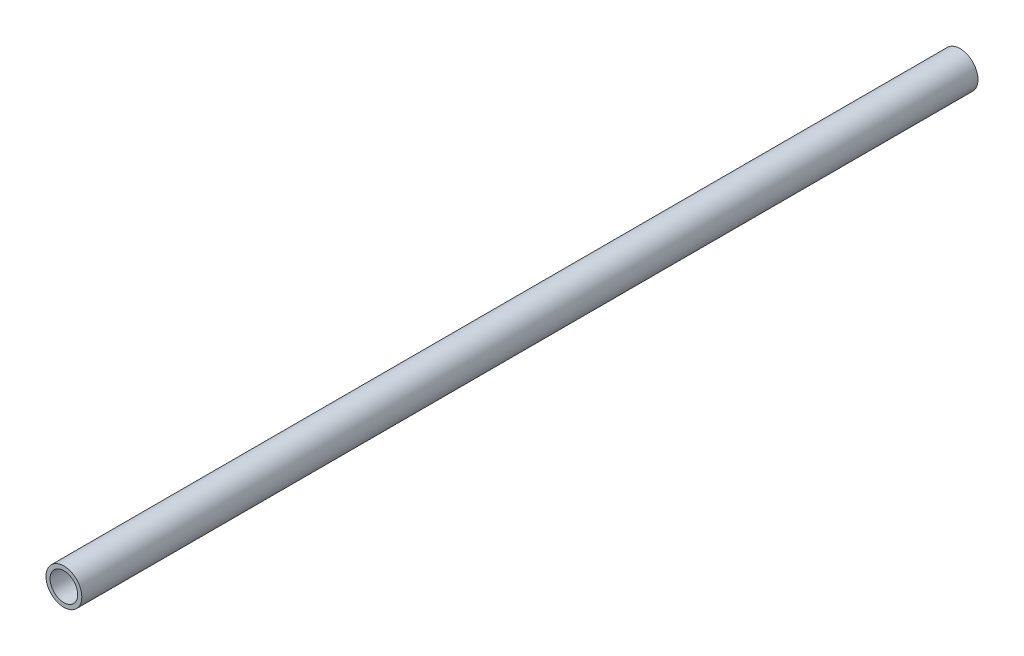
SolidWorks part; units mm, degrees
ref_plane "Front Plane" through (0, 0, 0) normal (0, 0, 1) x (1, 0, 0)
ref_plane "Top Plane" through (0, 0, 0) normal (0, 1, 0) x (1, 0, 0)
ref_plane "Right Plane" through (0, 0, 0) normal (1, 0, 0) x (0, 0, -1)
sketch "Sketch1" plane through (0, 0, 0) normal (0, 0, 1) x (1, 0, 0)
  circle A0 centre (-655.9929, -1.9195) radius 3.5
  circle A1 centre (-655.9929, -1.9195) radius 2.7
extrude "Boss-Extrude1" add sketch "Sketch1" along normal blind 175
